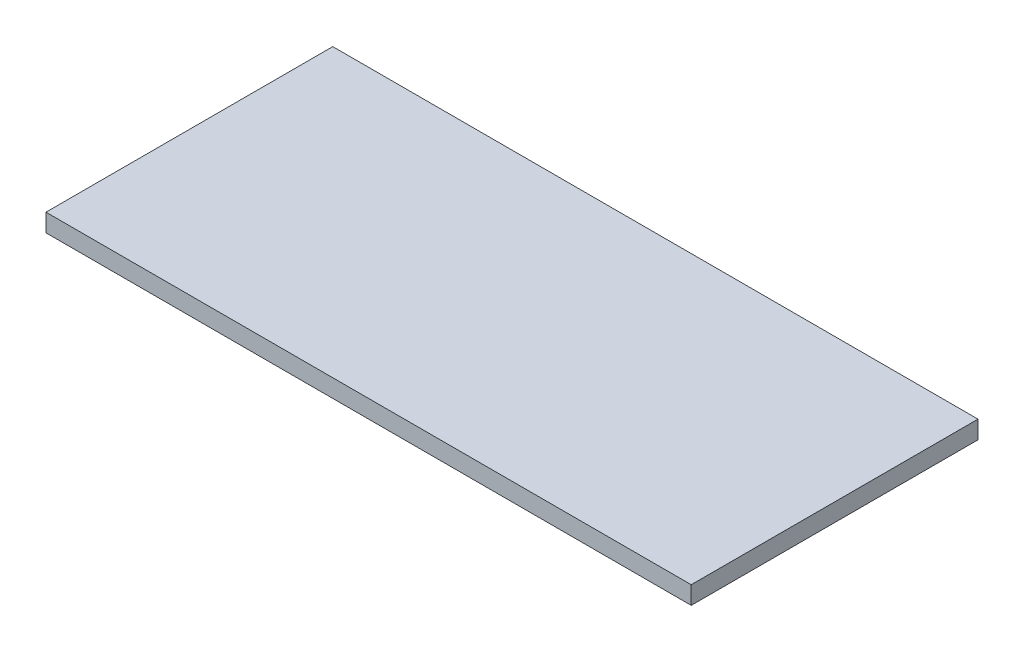
SolidWorks part; units mm, degrees
ref_plane "Front Plane" through (0, 0, 0) normal (0, 0, 1) x (1, 0, 0)
ref_plane "Top Plane" through (0, 0, 0) normal (0, 1, 0) x (1, 0, 0)
ref_plane "Right Plane" through (0, 0, 0) normal (1, 0, 0) x (0, 0, -1)
sketch "Sketch1" plane through (0, 0, 0) normal (0, 1, 0) x (1, 0, 0)
  line L1 (360, -160) -> (-360, -160)
  line L2 (360, -160) -> (360, 160)
  line L3 (360, 160) -> (-360, 160)
  line L4 (-360, -160) -> (-360, 160)
  line L5 (360, -160) -> (-360, 160) construction
  line L6 (360, 160) -> (-360, -160) construction
  point P0 (0, 0)
  dimension "D1" = 720
  dimension "D2" = 320
extrude "Boss-Extrude1" add sketch "Sketch1" along normal mid plane 20
